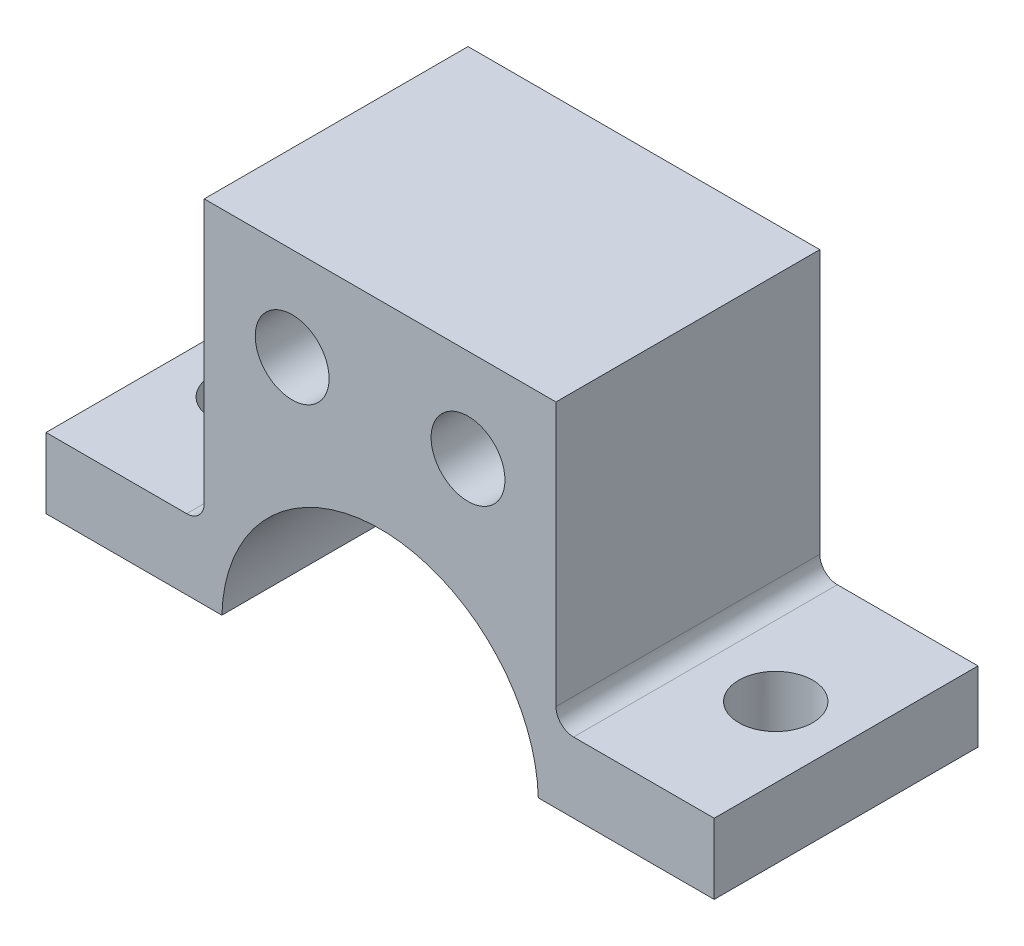
SolidWorks part; units mm, degrees
ref_plane "Front Plane" through (0, 0, 0) normal (0, 0, 1) x (1, 0, 0)
ref_plane "Top Plane" through (0, 0, 0) normal (0, 1, 0) x (1, 0, 0)
ref_plane "Right Plane" through (0, 0, 0) normal (1, 0, 0) x (0, 0, -1)
sketch "Sketch1" plane through (0, 0, 0) normal (0, 0, 1) x (1, 0, 0)
  line L0 (1.0035, -20) -> (-8.9965, -20)
  line L1 (-8.9965, -20) -> (-8.9965, -16)
  line L2 (-8.9965, -16) -> (0, -16)
  line L3 (0, -16) -> (0, 0)
  line L4 (0, 0) -> (20, 0)
  line L5 (20, -16) -> (20, 0)
  line L6 (20, -16) -> (28.9965, -16)
  line L7 (28.9965, -16) -> (28.9965, -20)
  line L8 (28.9965, -20) -> (18.9965, -20)
  arc A1 (18.9965, -20) -> (1.0035, -20) centre (10, -20.25) ccw
  circle A3 centre (5, -5.3) radius 2.1
  circle A4 centre (15, -5.3) radius 2.1
  dimension "D4" = 5
  dimension "D10" = 20
  dimension "D1" = 4.2
  dimension "D2" = 9
  dimension "D3" = 1.0035
  dimension "D5" = 10
  dimension "D6" = 15
  dimension "D7" = 28.9965
  dimension "D8" = 5.3
  dimension "D9" = 16
extrude "Boss-Extrude1" add sketch "Sketch1" along normal blind 15 contours A1 L8 L7 L6 L5 L4 L3 L2 L1 L0 A4 A3
sketch "Sketch2" plane through (0, -16, 0) normal (0, 1, 0) x (1, 0, 0)
  line L0 (28.9965, -15) -> (28.9965, 0) construction
  line L1 (20, -15) -> (28.9965, -15) construction
  line L2 (-8.9965, -15) -> (-8.9965, 0) construction
  circle A0 centre (-4.9965, -7.5) radius 2.1
  circle A1 centre (24.9965, -7.5) radius 2.1
  dimension "D1" = 4.2
  dimension "D2" = 4.2
  dimension "D3" = 4
  dimension "D4" = 7.5
  dimension "D5" = 4
extrude "Cut-Extrude1" cut sketch "Sketch2" against normal blind 10
fillet "Fillet2" radius 1 2 edges at (20, -16, 7.5) (0, -16, 7.5)
